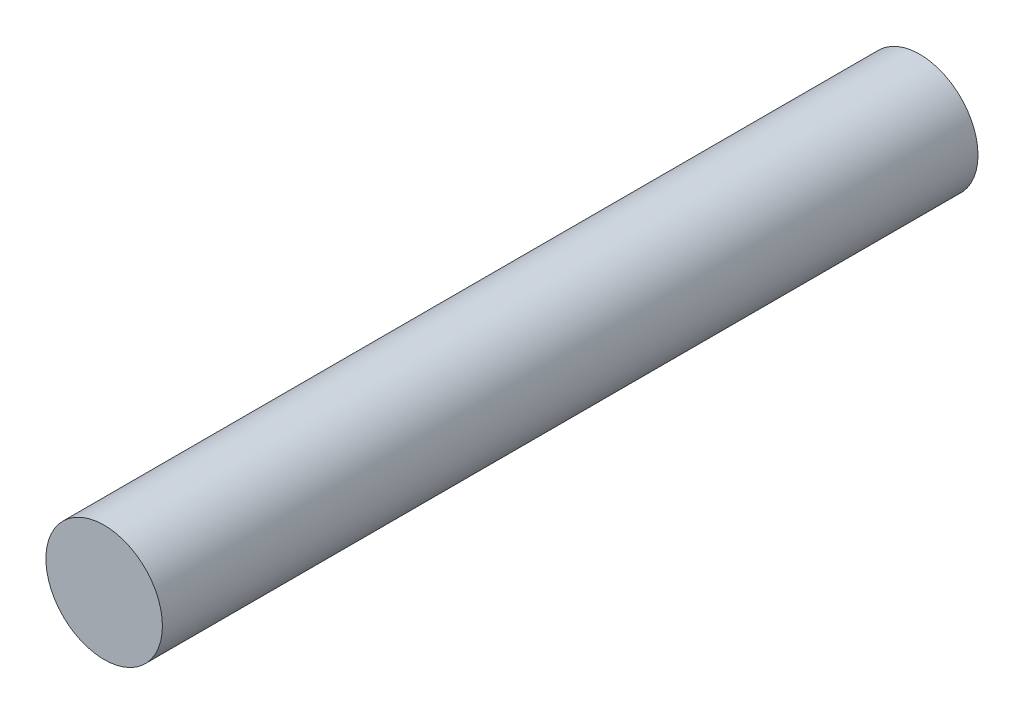
SolidWorks part; units mm, degrees
ref_plane "Front Plane" through (0, 0, 0) normal (0, 0, 1) x (1, 0, 0)
ref_plane "Top Plane" through (0, 0, 0) normal (0, 1, 0) x (1, 0, 0)
ref_plane "Right Plane" through (0, 0, 0) normal (1, 0, 0) x (0, 0, -1)
sketch "Sketch1" plane through (0, 0, 0) normal (0, 0, 1) x (1, 0, 0)
  circle A0 centre (0, 0) radius 2.5
  dimension "D1" = 5
extrude "Boss-Extrude1" add sketch "Sketch1" along normal blind 35
